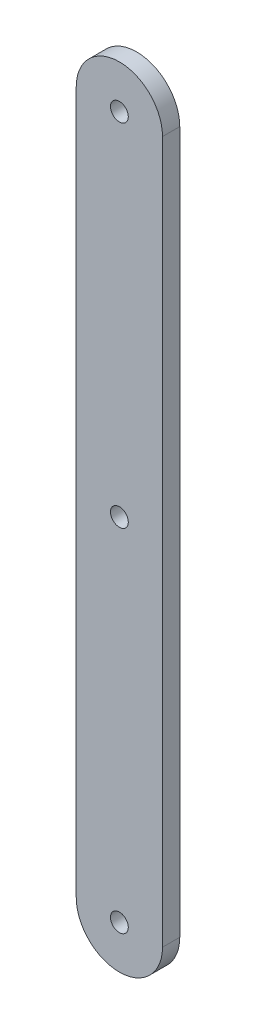
SolidWorks part; units mm, degrees
ref_plane "Alzado" through (0, 0, 0) normal (0, 0, 1) x (1, 0, 0)
ref_plane "Planta" through (0, 0, 0) normal (0, 1, 0) x (1, 0, 0)
ref_plane "Vista lateral" through (0, 0, 0) normal (1, 0, 0) x (0, 0, -1)
sketch "Croquis1" plane through (0, 0, 0) normal (0, 0, 1) x (1, 0, 0)
  line L0 (0, 0) -> (0, 122.06) construction
  line L1 (0, 0) -> (0, 122.06) construction
  line L2 (-7.5, 0) -> (-7.5, 122.06)
  line L3 (7.5, 0) -> (7.5, 122.06)
  circle A0 centre (0, 0) radius 1.55
  circle A1 centre (0, 122.06) radius 1.55
  arc A2 (-7.5, 0) -> (7.5, 0) centre (0, 0) ccw
  arc A3 (7.5, 122.06) -> (-7.5, 122.06) centre (0, 122.06) ccw
  circle A4 centre (0, 61.03) radius 1.55
  point P7 (0, 61.03)
  point P13 (7.5, 61.03)
  dimension "D2" = 3.1
  dimension "D3" = 3.1
  dimension "D1" = 3.1
  dimension "D4" = 15
  dimension "D5" = 61.03
extrude "Saliente-Extruir1" add sketch "Croquis1" along normal blind 3
sketch "Croquis2" plane through (0, 0, 3) normal (0, 0, 1) x (1, 0, 0)
  line L0 (0, 122.06) -> (0, 0) construction
